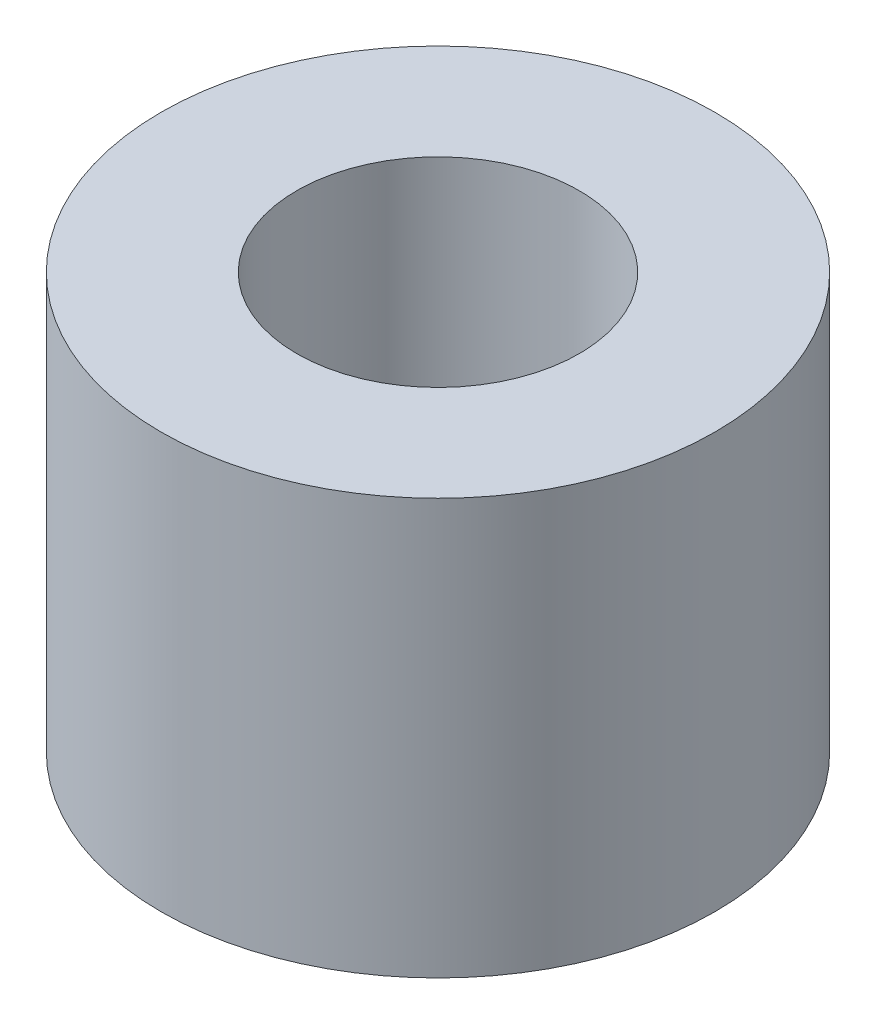
SolidWorks part; units mm, degrees
ref_plane "Ebene vorne" through (0, 0, 0) normal (0, 0, 1) x (1, 0, 0)
ref_plane "Ebene oben" through (0, 0, 0) normal (0, 1, 0) x (1, 0, 0)
ref_plane "Ebene rechts" through (0, 0, 0) normal (1, 0, 0) x (0, 0, -1)
sketch "Skizze1" plane through (0, 0, 0) normal (0, 1, 0) x (1, 0, 0)
  circle A0 centre (0, 0) radius 10
  dimension "D1" = 20
extrude "Zyl" add sketch "Skizze1" along normal blind 15
hole_wizard "M12 Gewindebohrung1" positions "Skizze3" profile "Skizze2" tap size "M12" standard "DIN"
sketch "Skizze3" plane through (0, 15, 0) normal (0, 1, 0) x (1, 0, 0)
  point P0 (0, 0)
sketch "Skizze2" plane through (0, 15, 0) normal (1, 0, 0) x (0, 0, 1)
  line L0 (0, 0) -> (0, 13.0644)
  line L1 (0, 13.0644) -> (5.1, 10)
  line L2 (5.1, 10) -> (5.1, 0)
  line L5 (5.1, 0) -> (0, 0)
  line L10 (0, 13.0644) -> (-5.1, 10) construction
  line L11 (0, -6.35) -> (0, 107.95) construction
  dimension "Bohrerdurchmesser" = 10.2
  dimension "Bohrungstiefe" = 10
  dimension "Spitzenwinkel" = 118
cosmetic thread "Bohrungsgewinde1"
